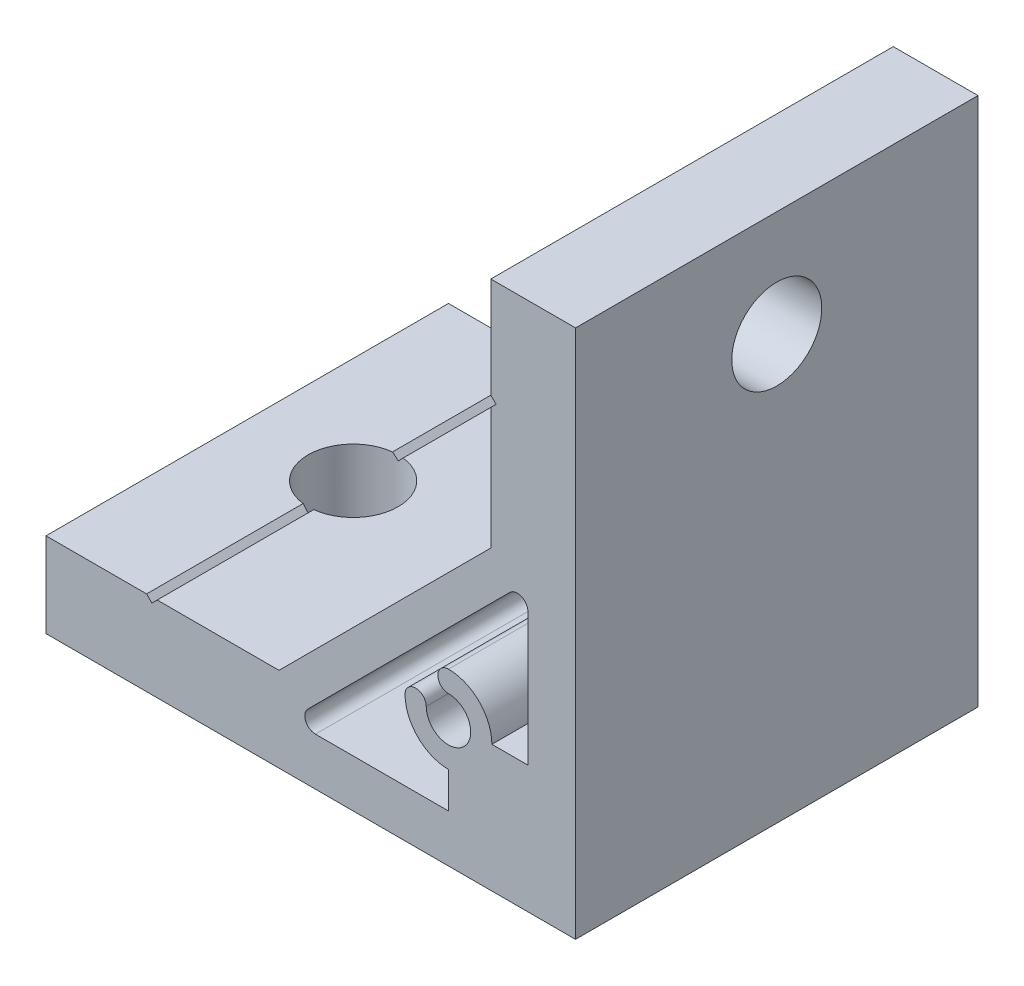
SolidWorks part; units mm, degrees
material "6063 T5"
ref_plane "Спереди" through (0, 0, 0) normal (0, 0, 1) x (1, 0, 0)
ref_plane "Сверху" through (0, 0, 0) normal (0, 1, 0) x (1, 0, 0)
ref_plane "Справа" through (0, 0, 0) normal (1, 0, 0) x (0, 0, -1)
sketch "Эскиз1" plane through (0, 0, 0) normal (0, 0, 1) x (1, 0, 0)
  line L0 (-50, 0) -> (0, 0)
  line L1 (0, 0) -> (0, 50)
  line L2 (0, 50) -> (-8, 50)
  line L3 (-8, 50) -> (-8, 40.5)
  line L4 (-8, 40.5) -> (-7.5, 40)
  line L5 (-7.5, 40) -> (-8, 39.5)
  line L6 (-8, 39.5) -> (-8, 28)
  line L7 (-8, 28) -> (-28, 8)
  line L8 (-28, 8) -> (-39.5, 8)
  line L9 (-39.5, 8) -> (-40, 7.5)
  line L10 (-40, 7.5) -> (-40.5, 8)
  line L11 (-40.5, 8) -> (-50, 8)
  line L12 (-50, 8) -> (-50, 0)
  line L13 (-4.5, 12) -> (-4.5, 24.5603)
  line L14 (-6.2071, 25.2674) -> (-25.2674, 6.2071)
  line L15 (-24.5603, 4.5) -> (-12, 4.5)
  line L16 (-12, 4.5) -> (-12, 7.9)
  line L17 (-7.9, 12) -> (-4.5, 12)
  arc A0 (-4.5, 24.5603) -> (-6.2071, 25.2674) centre (-5.5, 24.5603) ccw
  arc A1 (-25.2674, 6.2071) -> (-24.5603, 4.5) centre (-24.5603, 5.5) ccw
  arc A2 (-12, 7.9) -> (-16.1, 12) centre (-12, 12) cw
  arc A3 (-16.1, 12) -> (-14.1, 12) centre (-15.1, 12) cw
  arc A4 (-14.1, 12) -> (-12, 14.1) centre (-12, 12) ccw
  arc A5 (-12, 14.1) -> (-12, 16.1) centre (-12, 15.1) cw
  arc A6 (-12, 16.1) -> (-7.9, 12) centre (-12, 12) cw
  dimension "D6" = 4.2
  dimension "D7" = 1
  dimension "D9" = 1
  dimension "D1" = 50
  dimension "D2" = 8
  dimension "D3" = 135
  dimension "D4" = 12
  dimension "D5" = 12
  dimension "D8" = 28
  dimension "D10" = 3.2
  dimension "D11" = 4.5
  dimension "D12" = 40
  dimension "D13" = 1
extrude "Бобышка-Вытянуть1" add sketch "Эскиз1" along normal mid plane 38
sketch "Эскиз2" plane through (-8, 0, 0) normal (-1, 0, 0) x (0, 0, 1)
  line L0 (19, 40) -> (-19, 40) construction
  circle A0 centre (0, 40) radius 4.25
  dimension "D1" = 8.5
extrude "Вырез-Вытянуть1" cut sketch "Эскиз2" against normal through all
sketch "Эскиз3" plane through (0, 8, 0) normal (0, 1, 0) x (1, 0, 0)
  line L0 (-40, -19) -> (-40, 19) construction
  circle A0 centre (-40, 0) radius 4.25
  dimension "D1" = 8.5
extrude "Вырез-Вытянуть2" cut sketch "Эскиз3" against normal through all
